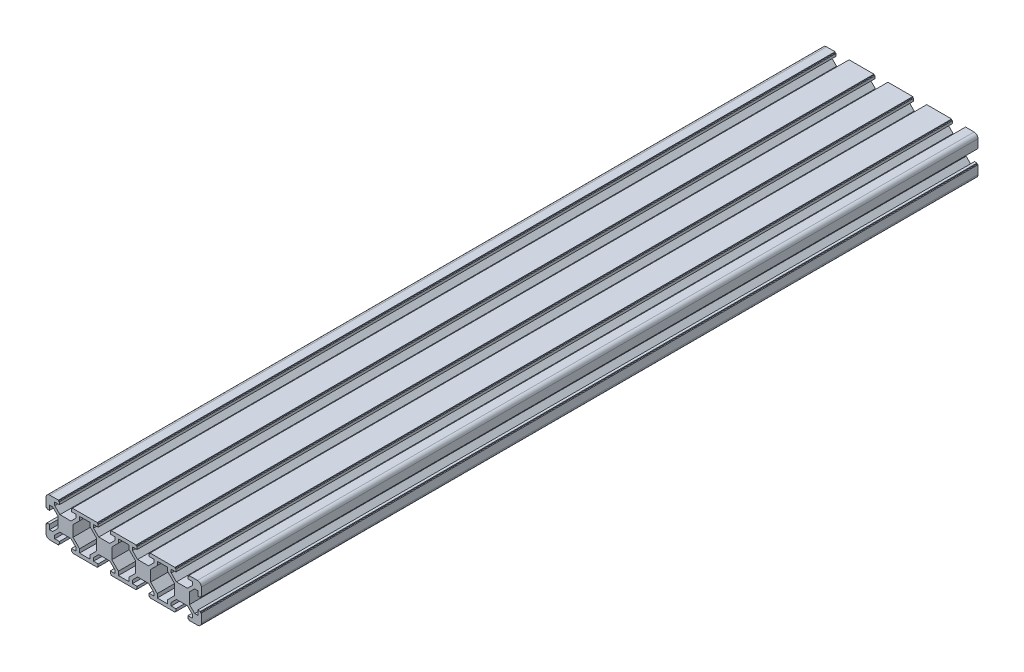
SolidWorks part; units mm, degrees
ref_plane "前视基准面" through (0, 0, 0) normal (0, 0, 1) x (1, 0, 0)
ref_plane "上视基准面" through (0, 0, 0) normal (0, 1, 0) x (1, 0, 0)
ref_plane "右视基准面" through (0, 0, 0) normal (1, 0, 0) x (0, 0, -1)
sketch "草图1" plane through (0, 0, 0) normal (0, 0, 1) x (1, 0, 0)
  line L0 (-7.4719, 0) -> (10.5099, 0) construction
  line L1 (0, 14.0818) -> (0, -12.6856) construction
  line L4 (-2.8393, 3.9) -> (2.8393, 3.9)
  line L5 (-3.9, 2.8393) -> (-3.9, -2.8393)
  line L6 (-2.8393, -3.9) -> (2.8393, -3.9)
  line L7 (3.9, 2.8393) -> (3.9, -2.8393)
  line L8 (-5.5, 6.5607) -> (-2.8393, 3.9)
  line L9 (-13.8543, 13.8543) -> (13.8543, -13.8543) construction
  line L10 (-6.5607, 5.5) -> (-3.9, 2.8393)
  line L11 (-5.5, 8.2) -> (-5.5, 6.5607)
  line L12 (7.3, 10) -> (3.6, 10)
  line L13 (-10, 14.605) -> (-10, -12.3784) construction
  line L14 (-3.6, 10) -> (-10, 10)
  line L15 (-8.2, 5.5) -> (-8.2, 3.1)
  line L16 (-9.5, 3.1) -> (-8.2, 3.1)
  line L17 (5.5, 8.2) -> (3.1, 8.2)
  line L18 (-3.6, 10) -> (-3.6, 9.5)
  line L19 (-3.6, 9.5) -> (-3.1, 9.5)
  line L20 (-3.1, 9.5) -> (-3.1, 8.2)
  line L21 (-5.5, 8.2) -> (-3.1, 8.2)
  line L22 (-9.5, 3.6) -> (-9.5, 3.1)
  line L23 (3.1, 9.5) -> (3.1, 8.2)
  line L24 (3.6, 9.5) -> (3.1, 9.5)
  line L25 (3.6, 10) -> (3.6, 9.5)
  line L26 (7.3, 10) -> (10, 10)
  line L27 (7.3, 8.2) -> (10, 8.2)
  line L28 (7.3, 8.2) -> (7.3, 6.2393)
  line L29 (5.5, 8.2) -> (5.5, 6.5607)
  line L30 (7.3, 6.2393) -> (3.9, 2.8393)
  line L31 (5.5, 6.5607) -> (2.8393, 3.9)
  line L32 (5.5, -6.5607) -> (2.8393, -3.9)
  line L33 (7.3, -6.2393) -> (3.9, -2.8393)
  line L34 (5.5, -8.2) -> (5.5, -6.5607)
  line L35 (7.3, -8.2) -> (7.3, -6.2393)
  line L36 (7.3, -8.2) -> (10, -8.2)
  line L37 (7.3, -10) -> (10, -10)
  line L38 (3.6, -10) -> (3.6, -9.5)
  line L39 (3.6, -9.5) -> (3.1, -9.5)
  line L40 (3.1, -9.5) -> (3.1, -8.2)
  line L41 (-8.2, -5.5) -> (-6.5607, -5.5)
  line L42 (-10, -3.6) -> (-10, -10)
  line L43 (-10, -3.6) -> (-9.5, -3.6)
  line L44 (-9.5, -3.6) -> (-9.5, -3.1)
  line L45 (-5.5, -8.2) -> (-3.1, -8.2)
  line L46 (5.5, -8.2) -> (3.1, -8.2)
  line L47 (-3.1, -9.5) -> (-3.1, -8.2)
  line L48 (-3.6, -9.5) -> (-3.1, -9.5)
  line L49 (-3.6, -10) -> (-3.6, -9.5)
  line L50 (7.3, -10) -> (3.6, -10)
  line L51 (-9.5, -3.1) -> (-8.2, -3.1)
  line L52 (-5.5, -6.5607) -> (-2.8393, -3.9)
  line L53 (30, 18.6284) -> (30, -23.4432) construction
  line L54 (17.1607, 3.9) -> (22.8393, 3.9)
  line L55 (16.1, 2.8393) -> (16.1, -2.8393)
  line L56 (17.1607, -3.9) -> (22.8393, -3.9)
  line L57 (23.9, 2.8393) -> (23.9, -2.8393)
  line L58 (14.5, 6.5607) -> (17.1607, 3.9)
  line L59 (12.7, 6.2393) -> (16.1, 2.8393)
  line L60 (14.5, 8.2) -> (14.5, 6.5607)
  line L61 (27.3, 10) -> (23.6, 10)
  line L62 (12.7, 8.2) -> (12.7, 6.2393)
  line L63 (12.7, 8.2) -> (10, 8.2)
  line L64 (12.7, 10) -> (10, 10)
  line L65 (25.5, 8.2) -> (23.1, 8.2)
  line L66 (16.4, 10) -> (16.4, 9.5)
  line L67 (16.4, 9.5) -> (16.9, 9.5)
  line L68 (16.9, 9.5) -> (16.9, 8.2)
  line L69 (14.5, 8.2) -> (16.9, 8.2)
  line L70 (12.7, 10) -> (16.4, 10)
  line L71 (23.1, 9.5) -> (23.1, 8.2)
  line L72 (23.6, 9.5) -> (23.1, 9.5)
  line L73 (23.6, 10) -> (23.6, 9.5)
  line L74 (27.3, 10) -> (30, 10)
  line L75 (27.3, 8.2) -> (30, 8.2)
  line L76 (27.3, 8.2) -> (27.3, 6.2393)
  line L77 (25.5, 8.2) -> (25.5, 6.5607)
  line L78 (27.3, 6.2393) -> (23.9, 2.8393)
  line L79 (25.5, 6.5607) -> (22.8393, 3.9)
  line L80 (25.5, -6.5607) -> (22.8393, -3.9)
  line L81 (27.3, -6.2393) -> (23.9, -2.8393)
  line L82 (25.5, -8.2) -> (25.5, -6.5607)
  line L83 (27.3, -8.2) -> (27.3, -6.2393)
  line L84 (27.3, -8.2) -> (30, -8.2)
  line L85 (27.3, -10) -> (30, -10)
  line L86 (23.6, -10) -> (23.6, -9.5)
  line L87 (23.6, -9.5) -> (23.1, -9.5)
  line L88 (23.1, -9.5) -> (23.1, -8.2)
  line L89 (12.7, -10) -> (16.4, -10)
  line L90 (14.5, -8.2) -> (16.9, -8.2)
  line L91 (16.9, -9.5) -> (16.9, -8.2)
  line L92 (16.4, -9.5) -> (16.9, -9.5)
  line L93 (16.4, -10) -> (16.4, -9.5)
  line L94 (25.5, -8.2) -> (23.1, -8.2)
  line L95 (12.7, -10) -> (10, -10)
  line L96 (12.7, -8.2) -> (10, -8.2)
  line L97 (12.7, -8.2) -> (12.7, -6.2393)
  line L98 (27.3, -10) -> (23.6, -10)
  line L99 (14.5, -8.2) -> (14.5, -6.5607)
  line L100 (12.7, -6.2393) -> (16.1, -2.8393)
  line L101 (14.5, -6.5607) -> (17.1607, -3.9)
  line L102 (12.5281, 0) -> (30.5099, 0) construction
  line L103 (37.1607, 3.9) -> (42.8393, 3.9)
  line L104 (36.1, 2.8393) -> (36.1, -2.8393)
  line L105 (37.1607, -3.9) -> (42.8393, -3.9)
  line L106 (43.9, 2.8393) -> (43.9, -2.8393)
  line L107 (34.5, 6.5607) -> (37.1607, 3.9)
  line L108 (32.7, 6.2393) -> (36.1, 2.8393)
  line L109 (34.5, 8.2) -> (34.5, 6.5607)
  line L110 (47.3, 10) -> (43.6, 10)
  line L111 (32.7, 8.2) -> (32.7, 6.2393)
  line L112 (32.7, 8.2) -> (30, 8.2)
  line L113 (32.7, 10) -> (30, 10)
  line L114 (45.5, 8.2) -> (43.1, 8.2)
  line L115 (36.4, 10) -> (36.4, 9.5)
  line L116 (36.4, 9.5) -> (36.9, 9.5)
  line L117 (36.9, 9.5) -> (36.9, 8.2)
  line L118 (34.5, 8.2) -> (36.9, 8.2)
  line L119 (32.7, 10) -> (36.4, 10)
  line L120 (43.1, 9.5) -> (43.1, 8.2)
  line L121 (43.6, 9.5) -> (43.1, 9.5)
  line L122 (43.6, 10) -> (43.6, 9.5)
  line L123 (47.3, 10) -> (50, 10)
  line L124 (47.3, 8.2) -> (50, 8.2)
  line L125 (47.3, 8.2) -> (47.3, 6.2393)
  line L126 (45.5, 8.2) -> (45.5, 6.5607)
  line L127 (47.3, 6.2393) -> (43.9, 2.8393)
  line L128 (45.5, 6.5607) -> (42.8393, 3.9)
  line L129 (45.5, -6.5607) -> (42.8393, -3.9)
  line L130 (47.3, -6.2393) -> (43.9, -2.8393)
  line L131 (45.5, -8.2) -> (45.5, -6.5607)
  line L132 (47.3, -8.2) -> (47.3, -6.2393)
  line L133 (47.3, -8.2) -> (50, -8.2)
  line L134 (47.3, -10) -> (50, -10)
  line L135 (43.6, -10) -> (43.6, -9.5)
  line L136 (43.6, -9.5) -> (43.1, -9.5)
  line L137 (43.1, -9.5) -> (43.1, -8.2)
  line L138 (32.7, -10) -> (36.4, -10)
  line L139 (34.5, -8.2) -> (36.9, -8.2)
  line L140 (36.9, -9.5) -> (36.9, -8.2)
  line L141 (36.4, -9.5) -> (36.9, -9.5)
  line L142 (36.4, -10) -> (36.4, -9.5)
  line L143 (45.5, -8.2) -> (43.1, -8.2)
  line L144 (32.7, -10) -> (30, -10)
  line L145 (32.7, -8.2) -> (30, -8.2)
  line L146 (32.7, -8.2) -> (32.7, -6.2393)
  line L147 (47.3, -10) -> (43.6, -10)
  line L148 (34.5, -8.2) -> (34.5, -6.5607)
  line L149 (32.7, -6.2393) -> (36.1, -2.8393)
  line L150 (34.5, -6.5607) -> (37.1607, -3.9)
  line L151 (32.5281, 0) -> (50.5099, 0) construction
  line L152 (57.1607, 3.9) -> (62.8393, 3.9)
  line L153 (56.1, 2.8393) -> (56.1, -2.8393)
  line L154 (57.1607, -3.9) -> (62.8393, -3.9)
  line L155 (66.5607, -5.5) -> (63.9, -2.8393)
  line L156 (54.5, 6.5607) -> (57.1607, 3.9)
  line L157 (52.7, 6.2393) -> (56.1, 2.8393)
  line L158 (54.5, 8.2) -> (54.5, 6.5607)
  line L159 (65.5, -8.2) -> (65.5, -6.5607)
  line L160 (52.7, 8.2) -> (52.7, 6.2393)
  line L161 (52.7, 8.2) -> (50, 8.2)
  line L162 (52.7, 10) -> (50, 10)
  line L163 (63.6, -10) -> (70, -10)
  line L164 (56.4, 10) -> (56.4, 9.5)
  line L165 (56.4, 9.5) -> (56.9, 9.5)
  line L166 (56.9, 9.5) -> (56.9, 8.2)
  line L167 (54.5, 8.2) -> (56.9, 8.2)
  line L168 (52.7, 10) -> (56.4, 10)
  line L169 (68.2, -5.5) -> (68.2, -3.1)
  line L170 (68.2, 5.5) -> (66.5607, 5.5)
  line L171 (70, 3.6) -> (70, 10)
  line L172 (70, 3.6) -> (69.5, 3.6)
  line L173 (65.5, -6.5607) -> (62.8393, -3.9)
  line L174 (69.5, -3.1) -> (68.2, -3.1)
  line L175 (63.6, -10) -> (63.6, -9.5)
  line L176 (63.6, -9.5) -> (63.1, -9.5)
  line L177 (63.1, -9.5) -> (63.1, -8.2)
  line L178 (65.5, -8.2) -> (63.1, -8.2)
  line L179 (69.5, -3.6) -> (69.5, -3.1)
  line L180 (70, -3.6) -> (69.5, -3.6)
  line L181 (70, -3.6) -> (70, -10)
  line L182 (68.2, -5.5) -> (66.5607, -5.5)
  line L183 (69.5, 3.6) -> (69.5, 3.1)
  line L184 (65.5, 8.2) -> (63.1, 8.2)
  line L185 (63.1, 9.5) -> (63.1, 8.2)
  line L186 (63.6, 9.5) -> (63.1, 9.5)
  line L187 (52.7, -10) -> (56.4, -10)
  line L188 (54.5, -8.2) -> (56.9, -8.2)
  line L189 (56.9, -9.5) -> (56.9, -8.2)
  line L190 (56.4, -9.5) -> (56.9, -9.5)
  line L191 (56.4, -10) -> (56.4, -9.5)
  line L192 (63.6, 10) -> (63.6, 9.5)
  line L193 (52.7, -10) -> (50, -10)
  line L194 (52.7, -8.2) -> (50, -8.2)
  line L195 (52.7, -8.2) -> (52.7, -6.2393)
  line L196 (69.5, 3.1) -> (68.2, 3.1)
  line L197 (54.5, -8.2) -> (54.5, -6.5607)
  line L198 (52.7, -6.2393) -> (56.1, -2.8393)
  line L199 (54.5, -6.5607) -> (57.1607, -3.9)
  line L200 (52.5281, 0) -> (70.5099, 0) construction
  line L201 (-10, 3.6) -> (-9.5, 3.6)
  line L202 (-10, 3.6) -> (-10, 10)
  line L203 (-8.2, 5.5) -> (-6.5607, 5.5)
  line L204 (-8.2, -5.5) -> (-8.2, -3.1)
  line L205 (-3.6, -10) -> (-10, -10)
  line L206 (-5.5, -8.2) -> (-5.5, -6.5607)
  line L207 (-6.5607, -5.5) -> (-3.9, -2.8393)
  line L208 (68.2, 5.5) -> (68.2, 3.1)
  line L209 (63.9, 2.8393) -> (63.9, -2.8393) [skipped]
  line L210 (67.3, 10) -> (63.6, 10) [skipped]
  line L211 (65.5, 8.2) -> (63.1, 8.2) [skipped]
  line L212 (63.1, 9.5) -> (63.1, 8.2) [skipped]
  line L213 (63.6, 9.5) -> (63.1, 9.5) [skipped]
  line L214 (63.6, 10) -> (63.6, 9.5) [skipped]
  line L215 (67.3, 10) -> (70, 10) [skipped]
  line L216 (67.3, 8.2) -> (70, 8.2) [skipped]
  line L217 (67.3, 8.2) -> (67.3, 6.2393) [skipped]
  line L218 (65.5, 8.2) -> (65.5, 6.5607) [skipped]
  line L219 (67.3, 6.2393) -> (63.9, 2.8393) [skipped]
  line L220 (65.5, 6.5607) -> (62.8393, 3.9) [skipped]
  line L221 (65.5, -6.5607) -> (62.8393, -3.9) [skipped]
  line L222 (67.3, -6.2393) -> (63.9, -2.8393) [skipped]
  line L223 (65.5, -8.2) -> (65.5, -6.5607) [skipped]
  line L224 (67.3, -8.2) -> (67.3, -6.2393) [skipped]
  line L225 (67.3, -8.2) -> (70, -8.2) [skipped]
  line L226 (67.3, -10) -> (70, -10) [skipped]
  line L227 (63.6, -10) -> (63.6, -9.5) [skipped]
  line L228 (63.6, -9.5) -> (63.1, -9.5) [skipped]
  line L229 (63.1, -9.5) -> (63.1, -8.2) [skipped]
  line L230 (65.5, -8.2) -> (63.1, -8.2) [skipped]
  line L231 (67.3, -10) -> (63.6, -10) [skipped]
  line L232 (63.6, 10) -> (70, 10)
  line L233 (65.5, 8.2) -> (65.5, 6.5607)
  line L234 (66.5607, 5.5) -> (63.9, 2.8393)
  line L235 (65.5, 6.5607) -> (62.8393, 3.9)
  line L236 (63.9, 2.8393) -> (63.9, -2.8393)
  dimension "D1" = 5.5
  dimension "D3" = 45
  dimension "D4" = 1.5
  dimension "D5" = 4
  dimension "D7" = 1.3
  dimension "D8" = 3.1
  dimension "D9" = 3.6
extrude "凸台-拉伸1" add sketch "草图1" along normal blind 400
fillet "圆角1" radius 2 4 edges at (70, -10, 200) (70, 10, 200) (-10, -10, 200) (-10, 10, 200)
